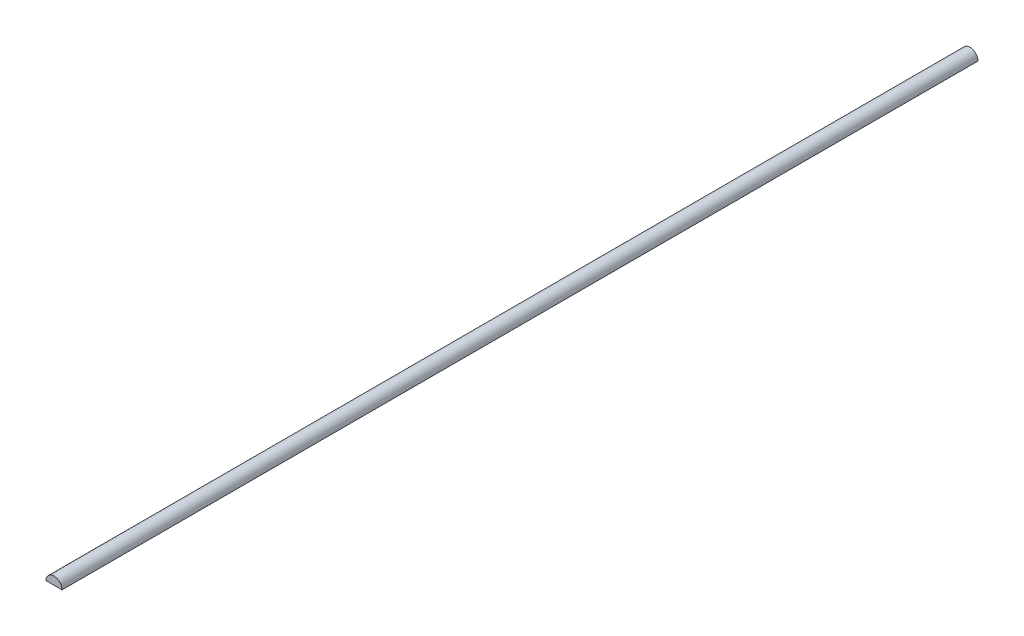
SolidWorks part; units mm, degrees
material "Rubber"
ref_plane "Front Plane" through (0, 0, 0) normal (0, 0, 1) x (1, 0, 0)
ref_plane "Top Plane" through (0, 0, 0) normal (0, 1, 0) x (1, 0, 0)
ref_plane "Right Plane" through (0, 0, 0) normal (1, 0, 0) x (0, 0, -1)
sketch "Sketch1" plane through (0, 0, 0) normal (0, 0, 1) x (1, 0, 0)
  line L0 (-12.7, 0) -> (12.7, 0)
  arc A0 (12.7, 0) -> (-12.7, 0) centre (0, 0) ccw
  dimension "D1" = 25.4
extrude "Boss-Extrude1" add sketch "Sketch1" along normal blind 1454.15 contours A0 L0
